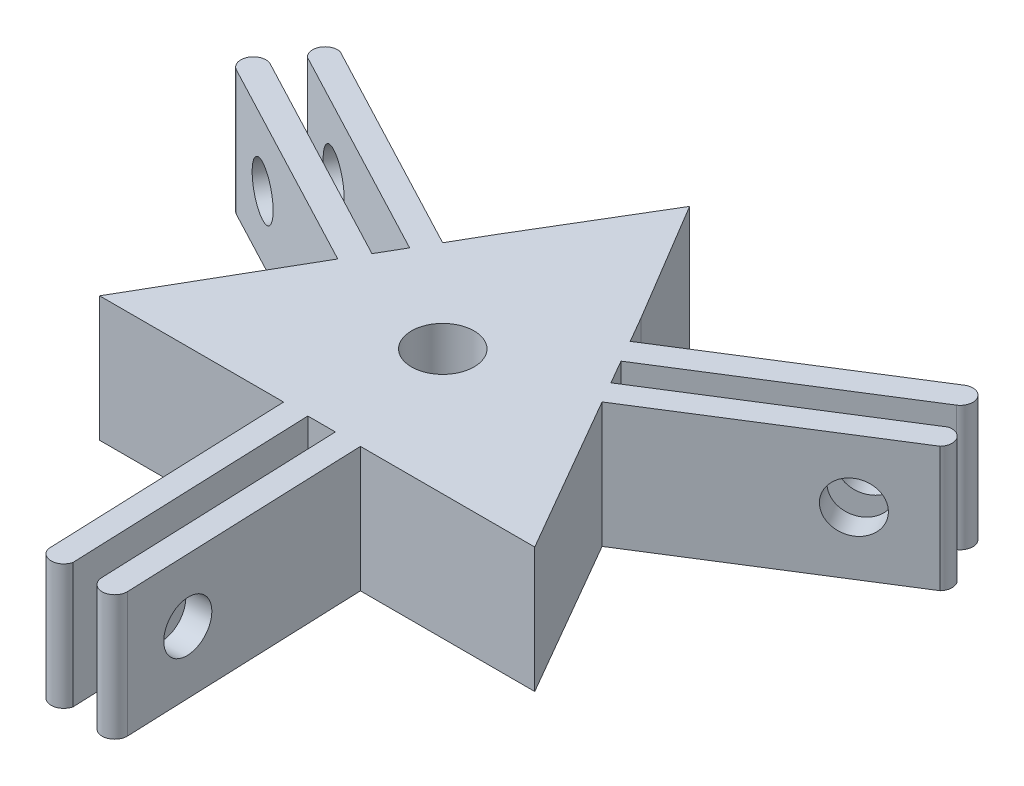
SolidWorks part; units mm, degrees
ref_plane "Front Plane" through (0, 0, 0) normal (0, 0, 1) x (1, 0, 0)
ref_plane "Top Plane" through (0, 0, 0) normal (0, 1, 0) x (1, 0, 0)
ref_plane "Right Plane" through (0, 0, 0) normal (1, 0, 0) x (0, 0, -1)
sketch "Sketch1" plane through (0, 0, 0) normal (0, 1, 0) x (1, 0, 0)
  line L0 (0, 0) -> (2.1154, 1.3323) construction
  line L1 (3.4294, -9.3936) -> (4.1979, -29.3788)
  line L2 (6.4203, 7.6668) -> (23.3438, 18.3249)
  line L3 (7.8455, 6.2007) -> (24.4096, 16.6325)
  line L4 (1.4472, -9.8947) -> (2.1994, -29.4556)
  line L5 (9.6881, 2.4781) -> (26.6116, 13.1362)
  line L6 (9.0115, 4.3351) -> (25.582, 14.7709)
  line L7 (-0.7514, -9.9717) -> (0.001, -29.5402)
  line L8 (-2.698, -9.6292) -> (-1.9295, -29.6144)
  line L9 (-9.8498, 1.7268) -> (-27.5417, 11.0539)
  line L10 (-9.2927, 3.694) -> (-26.609, 12.8231)
  line L11 (-8.2601, 5.6366) -> (-25.583, 14.7692)
  line L12 (-6.9901, 7.1511) -> (-24.6821, 16.4782)
  arc A0 (6.4203, 7.6668) -> (-6.9901, 7.1511) centre (0, 0) ccw
  circle A1 centre (0, 0) radius 2.5
  arc A2 (2.1994, -29.4556) -> (4.1979, -29.3788) centre (3.1986, -29.4172) ccw
  arc A3 (24.4096, 16.6325) -> (23.3438, 18.3249) centre (23.8767, 17.4787) ccw
  arc A4 (0.001, -29.5402) -> (-1.9295, -29.6144) centre (-0.9742, -29.3189) cw
  arc A5 (25.582, 14.7709) -> (26.6116, 13.1362) centre (25.878, 13.8157) cw
  arc A6 (9.0115, 4.3351) -> (7.8455, 6.2007) centre (0, 0) ccw
  arc A7 (-26.609, 12.8231) -> (-27.5417, 11.0539) centre (-27.0754, 11.9385) ccw
  arc A8 (-25.583, 14.7692) -> (-24.6821, 16.4782) centre (-24.9038, 15.5031) cw
  arc A9 (-9.8498, 1.7268) -> (-2.698, -9.6292) centre (0, 0) ccw
  arc A10 (-8.2601, 5.6366) -> (-9.2927, 3.694) centre (0, 0) ccw
  arc A11 (-0.7514, -9.9717) -> (1.4472, -9.8947) centre (0, 0) ccw
  arc A12 (3.4294, -9.3936) -> (9.6881, 2.4781) centre (0, 0) ccw
  point P7 (15.6157, 12.3163)
  point P15 (17.8539, 8.7623)
  point P39 (0, 0)
  dimension "D1" = 20
  dimension "D2" = 5
  dimension "D3" = 2
  dimension "D4" = 20
  dimension "D5" = 2.2
  dimension "D6" = 3
extrude "Boss-Extrude1" add sketch "Sketch1" along normal blind 10
sketch "Sketch2" plane through (3.0637, 0, -0.1178) normal (0.9993, 0, -0.0384) x (-0.0384, 0, -0.9993)
  line L0 (-29.5184, 10) -> (-29.5184, 0) construction
  line L1 (-29.5184, 0) -> (-9.5184, 0) construction
  circle A0 centre (-24.5184, 5) radius 2
  dimension "D1" = 5
  dimension "D3" = 4
  dimension "D2" = 5
extrude "Cut-Extrude1" cut sketch "Sketch2" against normal blind 10
pattern_circular "CirPattern1" count 3 over 360 about axis through (0, 10, 0) along (0, -1, 0) of "Cut-Extrude1"
sketch "Sketch3" plane through (0, 10, 0) normal (0, 1, 0) x (1, 0, 0)
  line L1 (11.5902, 0) -> (5.7951, 10.0374)
  line L2 (5.7951, 10.0374) -> (-5.7951, 10.0374)
  line L3 (-5.7951, 10.0374) -> (-11.5902, 0)
  line L4 (-11.5902, 0) -> (-5.7951, -10.0374)
  line L5 (-5.7951, -10.0374) -> (5.7951, -10.0374)
  line L6 (5.7951, -10.0374) -> (11.5902, 0)
  circle A0 centre (0, 0) radius 10.0374 construction
  circle A1 centre (0, 0) radius 2.5
extrude "Boss-Extrude3" add sketch "Sketch3" against normal blind 10
sketch "Sketch4" plane through (0, 10, 0) normal (0, 1, 0) x (1, 0, 0)
  line L0 (-5.7951, 10.0374) -> (0, 19.7244)
  line L1 (0, 19.7244) -> (5.7951, 10.0374)
  line L2 (-11.5902, 0) -> (-17.3852, -10.0374)
  line L3 (-5.7951, 10.0374) -> (-11.5902, 0) construction
  line L4 (-5.7951, -10.0374) -> (-17.3852, -10.0374)
  line L5 (-5.7951, -10.0374) -> (5.7951, -10.0374) construction
  line L6 (5.7951, -10.0374) -> (17.3852, -10.0374)
  line L7 (11.5902, 0) -> (17.3852, -10.0374)
  line L8 (11.5902, 0) -> (5.7951, 10.0374) construction
  line L9 (-5.7951, 10.0374) -> (-11.5902, 0)
  line L10 (5.7951, 10.0374) -> (11.5902, 0)
  line L11 (-5.7951, -10.0374) -> (5.7951, -10.0374)
  circle A0 centre (0, 0) radius 2.5008
extrude "Boss-Extrude4" add sketch "Sketch4" against normal blind 10
